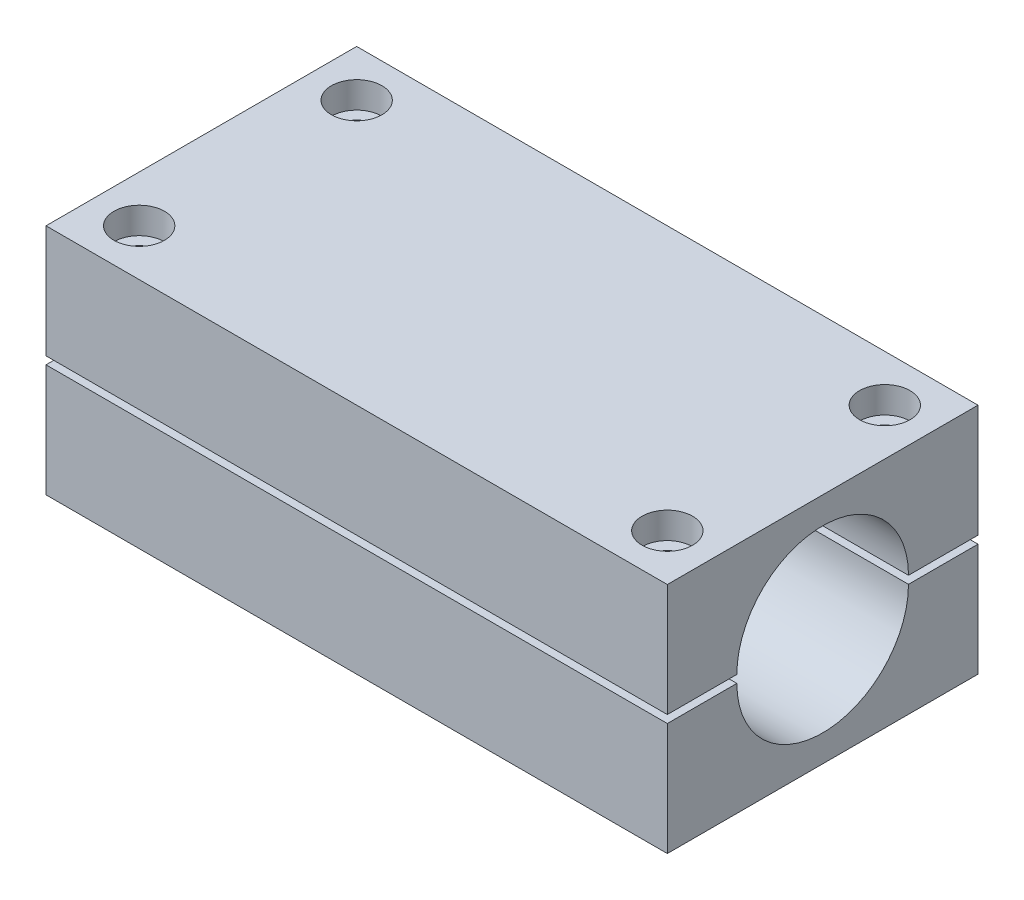
SolidWorks part; units mm, degrees
material "PLA"
ref_plane "Front Plane" through (0, 0, 0) normal (0, 0, 1) x (1, 0, 0)
ref_plane "Top Plane" through (0, 0, 0) normal (0, 1, 0) x (1, 0, 0)
ref_plane "Right Plane" through (0, 0, 0) normal (1, 0, 0) x (0, 0, -1)
sketch "Croquis1" plane through (0, 0, 0) normal (0, 1, 0) x (1, 0, 0)
  line L1 (-40, -20) -> (40, -20)
  line L2 (-40, -20) -> (-40, 20)
  line L3 (-40, 20) -> (40, 20)
  line L4 (40, -20) -> (40, 20)
  line L5 (-40, -20) -> (40, 20) construction
  line L6 (-40, 20) -> (40, -20) construction
  point P0 (0, 0)
  dimension "D1" = 80
  dimension "D2" = 40
extrude "Saliente-Extruir1" add sketch "Croquis1" along normal blind 30
sketch "Croquis2" plane through (-40, 0, 0) normal (-1, 0, 0) x (0, 0, 1)
  line L0 (-20, 0) -> (20, 30) construction
  line L1 (-20, 30) -> (20, 0) construction
  line L2 (-20, 15) -> (20, 15) construction
  line L3 (20, 30) -> (20, 0) construction
  line L4 (-20, 14.5) -> (20, 14.5) construction
  line L5 (-20, 15.5) -> (20, 15.5) construction
  line L6 (-11.05, 14.5) -> (11.05, 14.5)
  line L7 (11.05, 15.5) -> (-11.05, 15.5)
  arc A1 (-11.05, 15.5) -> (11.05, 15.5) centre (0, 15.5) cw
  arc A2 (-11.05, 14.5) -> (11.05, 14.5) centre (0, 14.5) ccw
  point P13 (0, 15)
  dimension "D1" = 0.5
  dimension "D3" = 11.05
  dimension "D2" = 0.5
extrude "Cortar-Extruir1" cut sketch "Croquis2" against normal through all
sketch "Croquis3" plane through (-40, 0, 0) normal (-1, 0, 0) x (0, 0, 1)
  line L0 (-20, 30) -> (-20, 0) construction
  line L1 (-20, 15.5) -> (20, 15.5)
  line L2 (-20, 15.5) -> (-20, 14.5)
  line L3 (-20, 14.5) -> (20, 14.5)
  line L4 (20, 15.5) -> (20, 14.5)
  line L5 (20, 30) -> (20, 0) construction
  line L6 (-11.05, 15.5) -> (11.05, 15.5) construction
  line L7 (0, -55) -> (0, 55) construction
  line L9 (-14, 13.5) -> (-14, 26) construction
  line L13 (14, 13.5) -> (14, 26) construction
  dimension "D1" = 1
  dimension "D2" = 6
extrude "Cortar-Extruir2" cut sketch "Croquis3" against normal through all
sketch "Croquis4" plane through (0, 30, 0) normal (0, 1, 0) x (1, 0, 0)
  line L0 (-40, 14) -> (40, 14) construction
  line L1 (40, -20) -> (40, 20) construction
  line L2 (-50, -14) -> (50, -14) construction
  line L3 (0, 20) -> (0, -20) construction
  line L4 (40, 20) -> (-40, 20) construction
  line L5 (-40, -20) -> (40, -20) construction
  line L7 (-34, 20) -> (-34, -20) construction
  line L8 (34, 20) -> (34, -20) construction
  line L9 (-40, 20) -> (-40, -20) construction
  point P0 (-40, 14)
  point P1 (-40, -14)
  point P23 (-40, 14)
  point P24 (-40, -14)
  dimension "D1" = 6
  dimension "D2" = 6
hole_wizard "Refrentado para tornillo con cabeza hueca de M31" positions "Croquis5" profile "Croquis6" counterbore size "M3" standard "DIN" end condition through all
sketch "Croquis5" plane through (0, 30, 0) normal (0, 1, 0) x (1, 0, 0)
  line L0 (-40, 14) -> (40, 14) construction
  line L1 (-34, 20) -> (-34, -20) construction
  line L2 (-50, -14) -> (50, -14) construction
  line L3 (34, 20) -> (34, -20) construction
  point P0 (-34, 14)
  point P6 (-34, -14)
  point P17 (34, 14)
  point P21 (34, -14)
sketch "Croquis6" plane through (-34, 30, -14) normal (1, 0, 0) x (0, 0, 1)
  line L0 (0, 0) -> (0, 30)
  line L1 (0, 30) -> (1.7, 30)
  line L3 (1.7, 30) -> (1.7, 3.4)
  line L4 (1.7, 3.4) -> (3.25, 3.4)
  line L5 (3.25, 3.4) -> (3.25, 0)
  line L7 (3.25, 0) -> (0, 0)
  line L11 (0, -6.35) -> (0, 107.95) construction
  dimension "Diámetro de taladro hasta el siguiente" = 3.4
  dimension "Profundidad de taladro hasta el siguiente" = 30
  dimension "Diámetro de refrentado" = 6.5
  dimension "Profundidad de refrentado" = 3.4
sketch "Croquis9" plane through (0, 0, 0) normal (0, -1, 0) x (1, 0, 0)
  line L1 (-30.5455, 14.2579) -> (-32.4961, 17.1206)
  line L2 (-32.4961, 17.1206) -> (-35.9506, 16.8627)
  line L3 (-35.9506, 16.8627) -> (-37.4545, 13.7421)
  line L4 (-37.4545, 13.7421) -> (-35.5039, 10.8794)
  line L5 (-35.5039, 10.8794) -> (-32.0494, 11.1373)
  line L6 (-32.0494, 11.1373) -> (-30.5455, 14.2579)
  circle A0 centre (-34, 14) radius 3 construction
  dimension "D1" = 6
extrude "Cortar-Extruir4" cut sketch "Croquis9" against normal blind 3
pattern_linear "MatrizL1" count 2 spacing 68 along (1, 0, 0) count 2 spacing 28 along (0, 0, -1) of "Cortar-Extruir4"
sketch "Croquis11" plane through (0, 30, 0) normal (0, 1, 0) x (1, 0, 0)
  line L0 (-30.75, 14) -> (-30.75, -14) construction
  line L1 (30.75, 14) -> (30.75, -14) construction
  circle A0 centre (-34, 14) radius 3.25 construction
  circle A1 centre (-34, 14) radius 3.25 construction
  circle A2 centre (-34, -14) radius 3.25 construction
  circle A3 centre (34, 14) radius 3.25 construction
  circle A4 centre (34, 14) radius 3.25 construction
  circle A5 centre (34, -14) radius 3.25 construction
  circle A6 centre (34, -14) radius 3.25 construction
